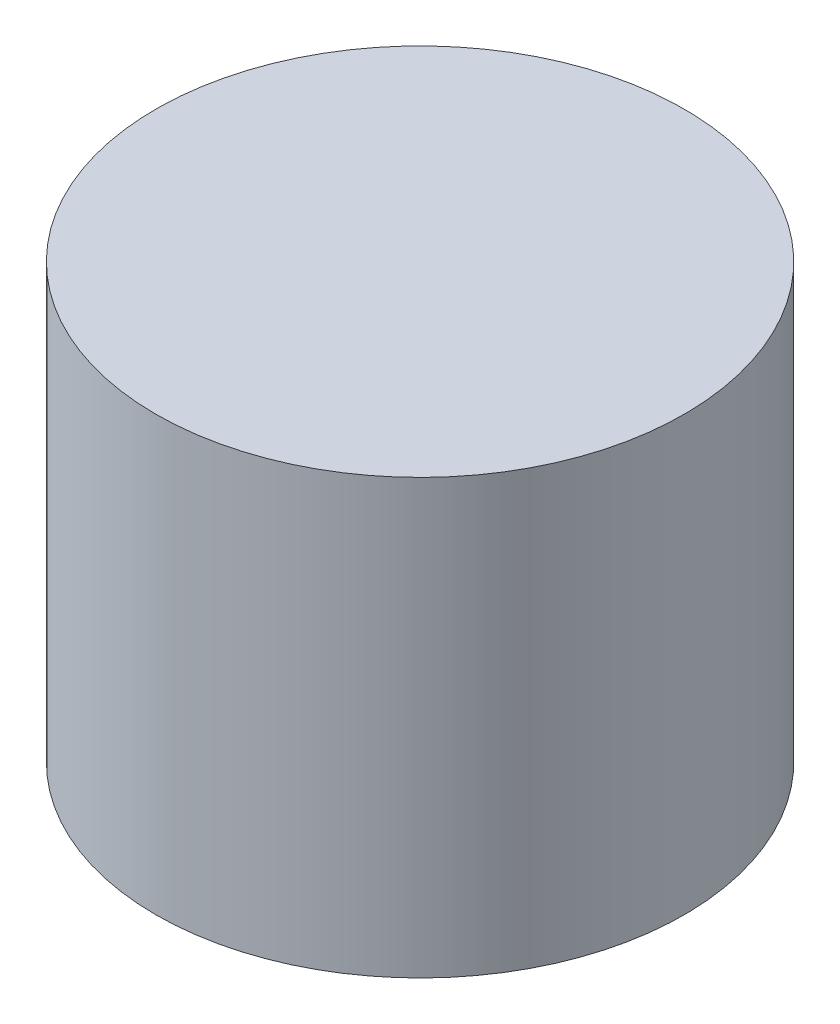
SolidWorks part; units mm, degrees
ref_plane "Front Plane" through (0, 0, 0) normal (0, 0, 1) x (1, 0, 0)
ref_plane "Top Plane" through (0, 0, 0) normal (0, 1, 0) x (1, 0, 0)
ref_plane "Right Plane" through (0, 0, 0) normal (1, 0, 0) x (0, 0, -1)
sketch "Sketch1" plane through (0, 0, 0) normal (0, 1, 0) x (1, 0, 0)
  circle A0 centre (0, 0) radius 32
  dimension "D1" = 64
extrude "Boss-Extrude1" add sketch "Sketch1" along normal mid plane 52.5
